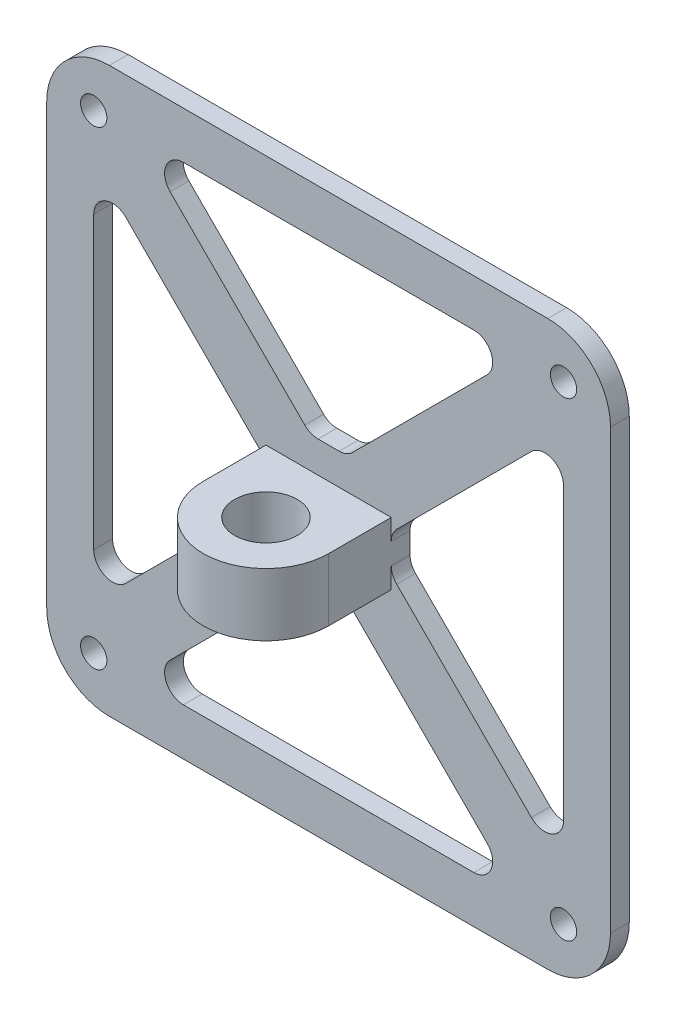
SolidWorks part; units mm, degrees
other "Marquage1"
sketch "Esquisse3" plane through (-5, -5, 30) normal (0, 0, 1) x (1, 0, 0)
ref_plane "Plan de face" through (0, 0, 0) normal (0, 0, 1) x (1, 0, 0)
ref_plane "Plan de dessus" through (0, 0, 0) normal (0, 1, 0) x (1, 0, 0)
ref_plane "Plan de droite" through (0, 0, 0) normal (1, 0, 0) x (0, 0, -1)
sketch "Esquisse1" plane through (0, 0, 0) normal (0, 0, 1) x (1, 0, 0)
  line L10 (-35, -45) -> (35, -45)
  line L14 (-45, -35) -> (-45, 35)
  line L16 (-35, 45) -> (35, 45)
  line L17 (45, -35) -> (45, 35)
  line L19 (-45, -45) -> (45, 45) construction
  line L21 (-45, 45) -> (45, -45) construction
  circle A8 centre (-37.5, 37.5) radius 2.1
  circle A9 centre (37.5, 37.5) radius 2.1
  circle A10 centre (37.5, -37.5) radius 2.1
  circle A11 centre (-37.5, -37.5) radius 2.1
  arc A12 (-35, -45) -> (-45, -35) centre (-35, -35) cw
  arc A13 (35, -45) -> (45, -35) centre (35, -35) ccw
  arc A14 (35, 45) -> (45, 35) centre (35, 35) cw
  arc A15 (-45, 35) -> (-35, 45) centre (-35, 35) cw
  point P0 (0, 0)
  point P14 (0, 0)
  point P15 (0, 0)
  point P16 (0, 0)
  point P17 (0, 0)
  dimension "D3" = 90
  dimension "D4" = 10
  dimension "D1" = 4.2
  dimension "D2" = 75
extrude "Boss.-Extru.1" add sketch "Esquisse1" along normal blind 3
sketch "Esquisse4" plane through (0, 45, 123.3162) normal (0, 1, 0) x (1, 0, 0)
  line L0 (10, 120.3162) -> (10, 110.3162)
  line L2 (-10, 110.3162) -> (-10, 120.3162)
  line L3 (10, 120.3162) -> (-10, 120.3162)
  line L5 (-10, 110.3162) -> (10, 110.3162) construction
  line L6 (35, 120.3162) -> (-35, 120.3162) construction
  circle A0 centre (0, 110.3162) radius 5
  arc A1 (10, 110.3162) -> (-10, 110.3162) centre (0, 110.3162) cw
  point P3 (0, 123.3162)
  point P6 (0, 0)
  point P9 (0, 120.3162)
  point P12 (0, 120.3162)
  point P14 (0, 113.3162)
  dimension "D2" = 10
  dimension "D1" = 10
  dimension "D3" = 20
ref_plane "Plan2" [suppressed] through (0, 57.45, 0) normal (0, 1, 0) x (1, 0, 0)
extrude "Boss.-Extru.2" add sketch "Esquisse4" along normal blind 10 from offset 50 offset against normal yes
sketch "Esquisse5" plane through (0, 0, 3) normal (0, 0, 1) x (1, 0, 0)
  line L0 (0, 45) -> (0, -45) construction
  line L1 (35, 45) -> (-35, 45) construction
  line L2 (-35, -45) -> (35, -45) construction
  line L3 (-37.5, -37.5) -> (37.5, 37.5) construction
  line L4 (-45, 35) -> (-45, -35) construction
  line L5 (-45, 0) -> (45, 0) construction
  line L6 (45, -35) -> (45, 35) construction
  line L7 (-37.5, 37.5) -> (37.5, -37.5) construction
  line L8 (-23.1863, 37.5) -> (23.1863, 37.5)
  line L9 (25.3076, 32.3787) -> (3.8076, 10.8787)
  line L10 (1.6863, 10) -> (-1.6863, 10)
  line L11 (-25.3076, 32.3787) -> (-3.8076, 10.8787)
  line L12 (-32.3787, -25.3076) -> (-10.8787, -3.8076)
  line L13 (-37.5, 23.1863) -> (-37.5, -23.1863)
  line L14 (-32.3787, 25.3076) -> (-10.8787, 3.8076)
  line L15 (10, 5) -> (-10, 5) construction
  line L16 (-10, -1.6863) -> (-10, 1.6863)
  line L17 (32.3787, 25.3076) -> (10.8787, 3.8076)
  line L18 (37.5, -23.1863) -> (37.5, 23.1863)
  line L19 (32.3787, -25.3076) -> (10.8787, -3.8076)
  line L20 (10, 1.6863) -> (10, -1.6863)
  line L21 (23.1863, -37.5) -> (-23.1863, -37.5)
  line L22 (25.3076, -32.3787) -> (3.8076, -10.8787)
  line L23 (-1.6863, -10) -> (1.6863, -10)
  line L24 (-25.3076, -32.3787) -> (-3.8076, -10.8787)
  arc A0 (23.1863, 37.5) -> (25.3076, 32.3787) centre (23.1863, 34.5) cw
  arc A1 (3.8076, 10.8787) -> (1.6863, 10) centre (1.6863, 13) cw
  arc A2 (-3.8076, 10.8787) -> (-1.6863, 10) centre (-1.6863, 13) ccw
  arc A3 (-25.3076, 32.3787) -> (-23.1863, 37.5) centre (-23.1863, 34.5) cw
  arc A4 (-37.5, -23.1863) -> (-32.3787, -25.3076) centre (-34.5, -23.1863) ccw
  arc A5 (-32.3787, 25.3076) -> (-37.5, 23.1863) centre (-34.5, 23.1863) ccw
  arc A6 (-10.8787, -3.8076) -> (-10, -1.6863) centre (-13, -1.6863) ccw
  arc A7 (-10.8787, 3.8076) -> (-10, 1.6863) centre (-13, 1.6863) cw
  arc A8 (37.5, 23.1863) -> (32.3787, 25.3076) centre (34.5, 23.1863) ccw
  arc A9 (32.3787, -25.3076) -> (37.5, -23.1863) centre (34.5, -23.1863) ccw
  arc A10 (10.8787, 3.8076) -> (10, 1.6863) centre (13, 1.6863) ccw
  arc A11 (10.8787, -3.8076) -> (10, -1.6863) centre (13, -1.6863) cw
  arc A12 (-23.1863, -37.5) -> (-25.3076, -32.3787) centre (-23.1863, -34.5) cw
  arc A13 (25.3076, -32.3787) -> (23.1863, -37.5) centre (23.1863, -34.5) cw
  arc A14 (3.8076, -10.8787) -> (1.6863, -10) centre (1.6863, -13) ccw
  arc A15 (-3.8076, -10.8787) -> (-1.6863, -10) centre (-1.6863, -13) cw
  point P25 (0, 10)
  point P26 (0, 37.5)
  point P28 (30.4289, 37.5)
  point P33 (2.9289, 10)
  point P36 (-2.9289, 10)
  point P39 (-30.4289, 37.5)
  dimension "D4" = 3
  dimension "D1" = 5
  dimension "D2" = 5
  dimension "D3" = 7.5
extrude "Enlèv. mat.-Extru.1" cut sketch "Esquisse5" against normal blind 10
